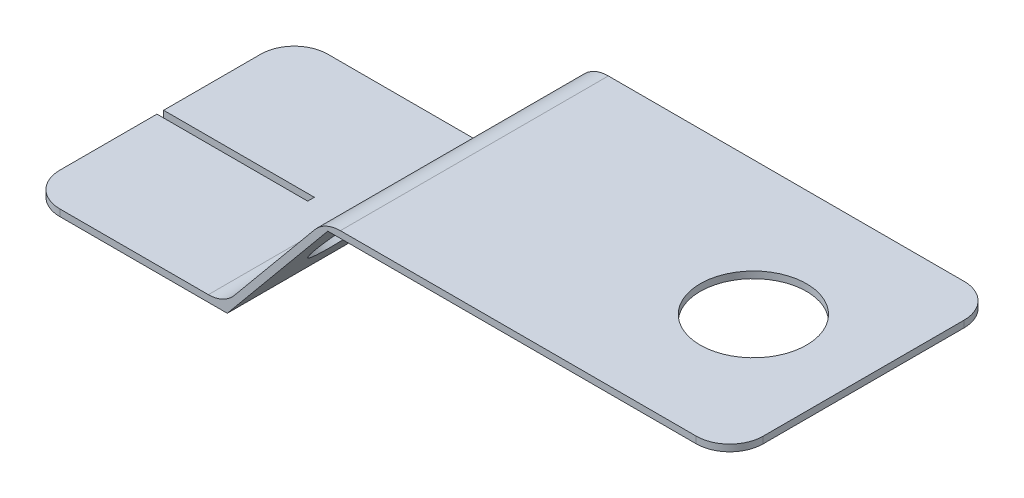
SolidWorks part; units mm, degrees
ref_plane "Front Plane" through (0, 0, 0) normal (0, 0, 1) x (1, 0, 0)
ref_plane "Top Plane" through (0, 0, 0) normal (0, 1, 0) x (1, 0, 0)
ref_plane "Right Plane" through (0, 0, 0) normal (1, 0, 0) x (0, 0, -1)
sketch "Sketch1" plane through (0, 0, 0) normal (0, 0, 1) x (1, 0, 0)
  line L0 (0, 0) -> (6, 0)
  line L1 (6, 0) -> (9, 3.625)
  line L2 (9, 3.625) -> (21, 3.625)
  line L3 (0, 0.2) -> (5.9059, 0.2)
  line L4 (5.9059, 0.2) -> (8.9059, 3.825)
  line L5 (8.9059, 3.825) -> (21, 3.825)
  line L6 (0, 0.2) -> (0, 0)
  line L7 (21, 3.825) -> (21, 3.625)
  dimension "D1" = 6
  dimension "D2" = 3.625
  dimension "D3" = 3
  dimension "D4" = 12
  dimension "D5" = 0.2
extrude "Boss-Extrude1" add sketch "Sketch1" along normal mid plane 8
sketch "Sketch2" plane through (0, 3.825, 0) normal (0, 1, 0) x (1, 0, 0)
  line L0 (8.9059, -4) -> (8.9059, 4) construction
  circle A0 centre (17.7059, 0) radius 1.5875
  dimension "D1" = 3.175
  dimension "D2" = 8.8
extrude "Cut-Extrude1" cut sketch "Sketch2" against normal blind 10 contours A0
fillet "Fillet1" radius 1 4 edges at (21, 3.725, -4) (21, 3.725, 4) (0, 0.1, -4) (0, 0.1, 4)
sketch "Sketch3" plane through (0, 0.2, 0) normal (0, 1, 0) x (1, 0, 0)
  line L0 (0, -3) -> (0, 3) construction
  line L1 (0, 0.1) -> (4.5, 0.1)
  line L2 (0, 0.1) -> (0, -0.1)
  line L3 (0, -0.1) -> (4.5, -0.1)
  line L4 (4.5, 0.1) -> (4.5, -0.1)
  point P6 (0, 0)
  dimension "D1" = 4.5
  dimension "D2" = 0.2
extrude "Cut-Extrude2" cut sketch "Sketch3" against normal blind 10
fillet "Fillet2" radius 1 2 edges at (5.9059, 0.2, 0) (8.9059, 3.825, 0)
sketch "Sketch4" plane through (3.407, -2.8196, 0) normal (-0.7704, 0.6376, 0) x (0, 0, 1)
  line L0 (-4, 8.1544) -> (-4, 4.3899) construction
  circle A0 centre (-1.75, 6.2722) radius 1.1906
  point P4 (-4, 6.2722)
  dimension "D1" = 2.3813
  dimension "D2" = 1.75
extrude "Cut-Extrude3" cut sketch "Sketch4" against normal blind 10
mirror "Mirror1" about plane through (0, 0, 0) normal (0, 0, 1) of "Cut-Extrude3"
